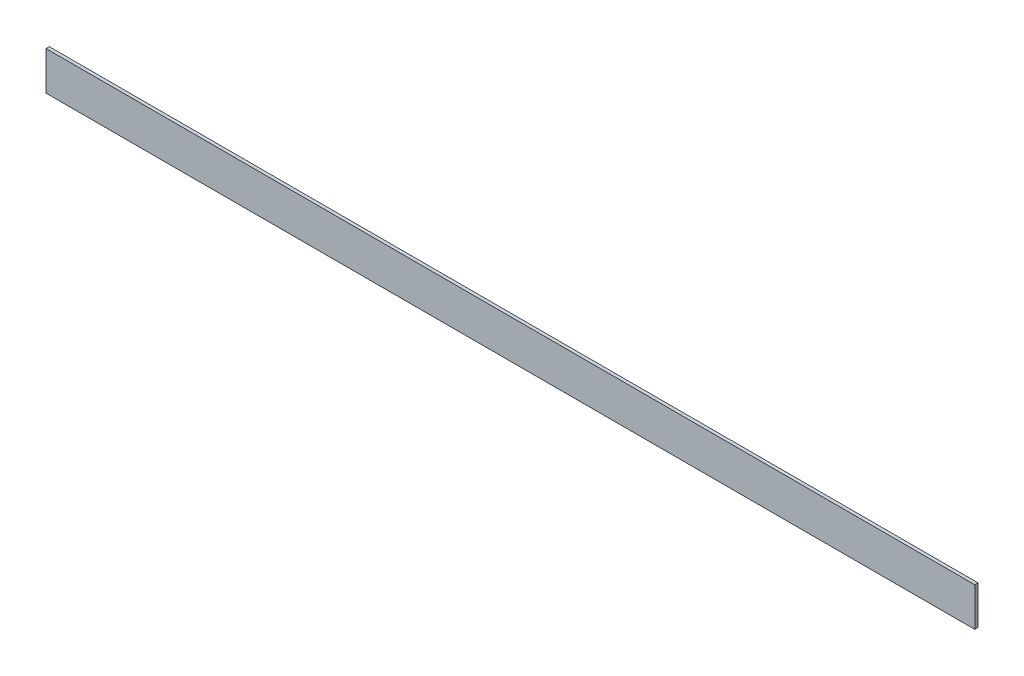
SolidWorks part; units mm, degrees
material "PVC 0.007 Plasticized"
ref_plane "Front Plane" through (0, 0, 0) normal (0, 0, 1) x (1, 0, 0)
ref_plane "Top Plane" through (0, 0, 0) normal (0, 1, 0) x (1, 0, 0)
ref_plane "Right Plane" through (0, 0, 0) normal (1, 0, 0) x (0, 0, -1)
sketch "Sketch1" plane through (0, 0, 0) normal (1, 0, 0) x (0, 0, -1)
  line L1 (-3.175, -38.1) -> (3.175, -38.1)
  line L2 (-3.175, -38.1) -> (-3.175, 38.1)
  line L3 (-3.175, 38.1) -> (3.175, 38.1)
  line L4 (3.175, -38.1) -> (3.175, 38.1)
  line L5 (-3.175, -38.1) -> (3.175, 38.1) construction
  line L6 (-3.175, 38.1) -> (3.175, -38.1) construction
  point P0 (0, 0)
  dimension "D1" = 76.2
  dimension "D2" = 6.35
extrude "Boss-Extrude1" add sketch "Sketch1" along normal blind 1828.8
equation "\"D2@Sketch1\"=1in/4"
